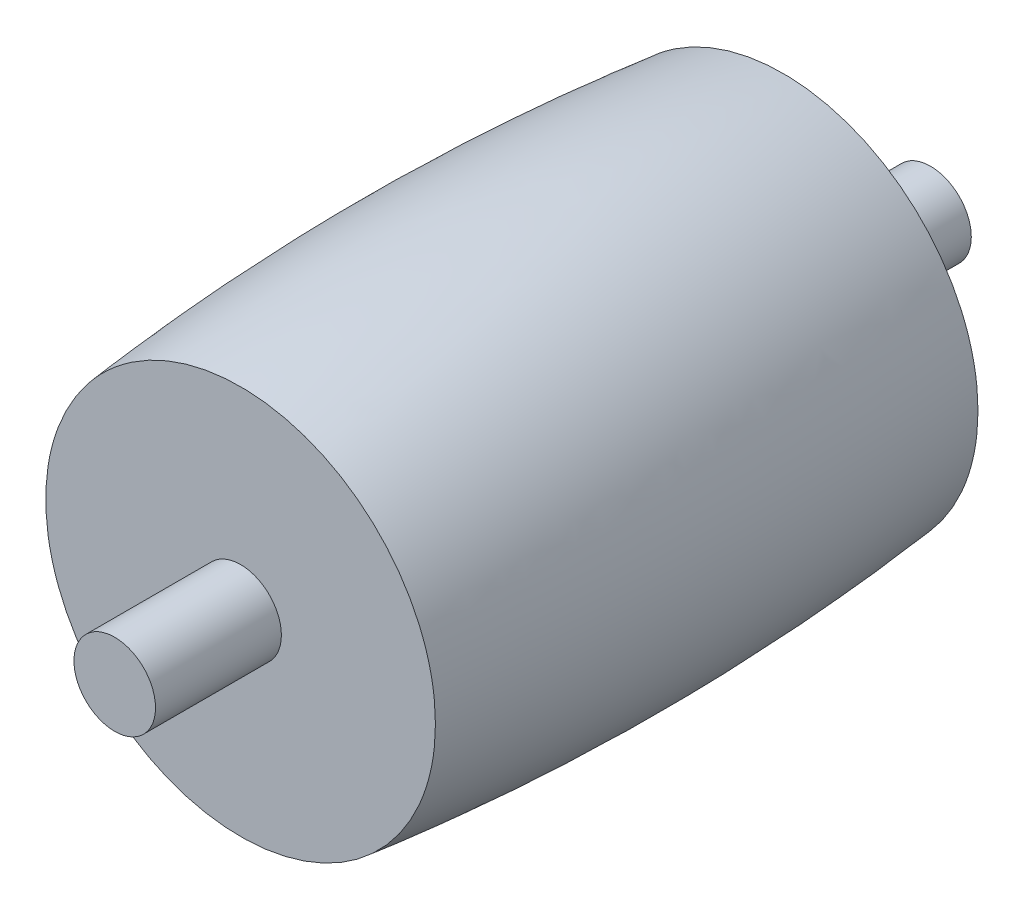
SolidWorks part; units mm, degrees
ref_plane "前视基准面" through (0, 0, 0) normal (0, 0, 1) x (1, 0, 0)
ref_plane "上视基准面" through (0, 0, 0) normal (0, 1, 0) x (1, 0, 0)
ref_plane "右视基准面" through (0, 0, 0) normal (1, 0, 0) x (0, 0, -1)
sketch "草图1" plane through (0, 0, 0) normal (0, 0, 1) x (1, 0, 0)
  circle A0 centre (0, 0) radius 1
  dimension "D1" = 2
extrude "凸台-拉伸1" add sketch "草图1" along normal blind 20 contours A0
ref_plane "基准面1" through (0, 0, 10) normal (0, 0, 1) x (1, 0, 0)
sketch "草图2" plane through (0, 0, 0) normal (0, 1, 0) x (1, 0, 0)
  line L0 (0, -3.6128) -> (4.7769, -3.6128)
  line L1 (0, -16.9143) -> (4.7769, -16.9143)
  line L2 (0, -3.6128) -> (0, -16.9143)
  line L3 (-1.1, -10) -> (1.1, -10) construction
  spline S0 degree 2 poles (4.7769, -3.6128) (5.5059, -10.262) (4.7769, -16.9143) knots 0 0 0 1 1 1
  point P6 (-0.2546, -3.6559)
  point P7 (0, 0)
sketch "草图3" plane through (0, 0, 10) normal (0, 0, 1) x (1, 0, 0)
  circle A0 centre (0, 0) radius 0.7516
sweep "扫描2" add profiles "草图2" path "草图3"
